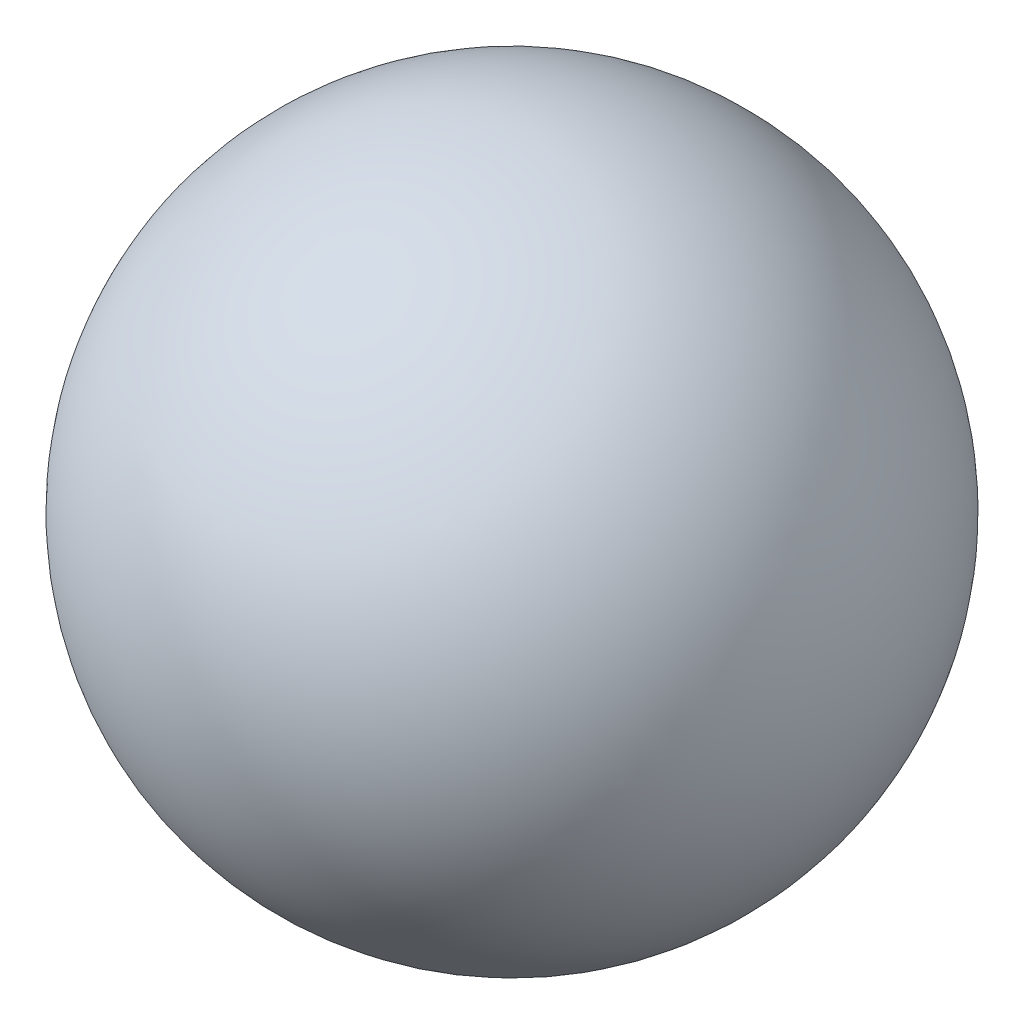
SolidWorks part; units mm, degrees
material "Titanium"
ref_plane "Front Plane" through (0, 0, 0) normal (0, 0, 1) x (1, 0, 0)
ref_plane "Top Plane" through (0, 0, 0) normal (0, 1, 0) x (1, 0, 0)
ref_plane "Right Plane" through (0, 0, 0) normal (1, 0, 0) x (0, 0, -1)
sketch "Sketch1" plane through (0, 0, 0) normal (0, 1, 0) x (1, 0, 0)
  line L0 (0, 0) -> (-400, 0)
  arc A0 (-400, 0) -> (0, 0) centre (-200, 0) cw
  dimension "D1" = 400
revolve "Revolve1" add sketch "Sketch1" angle 360 about L0
